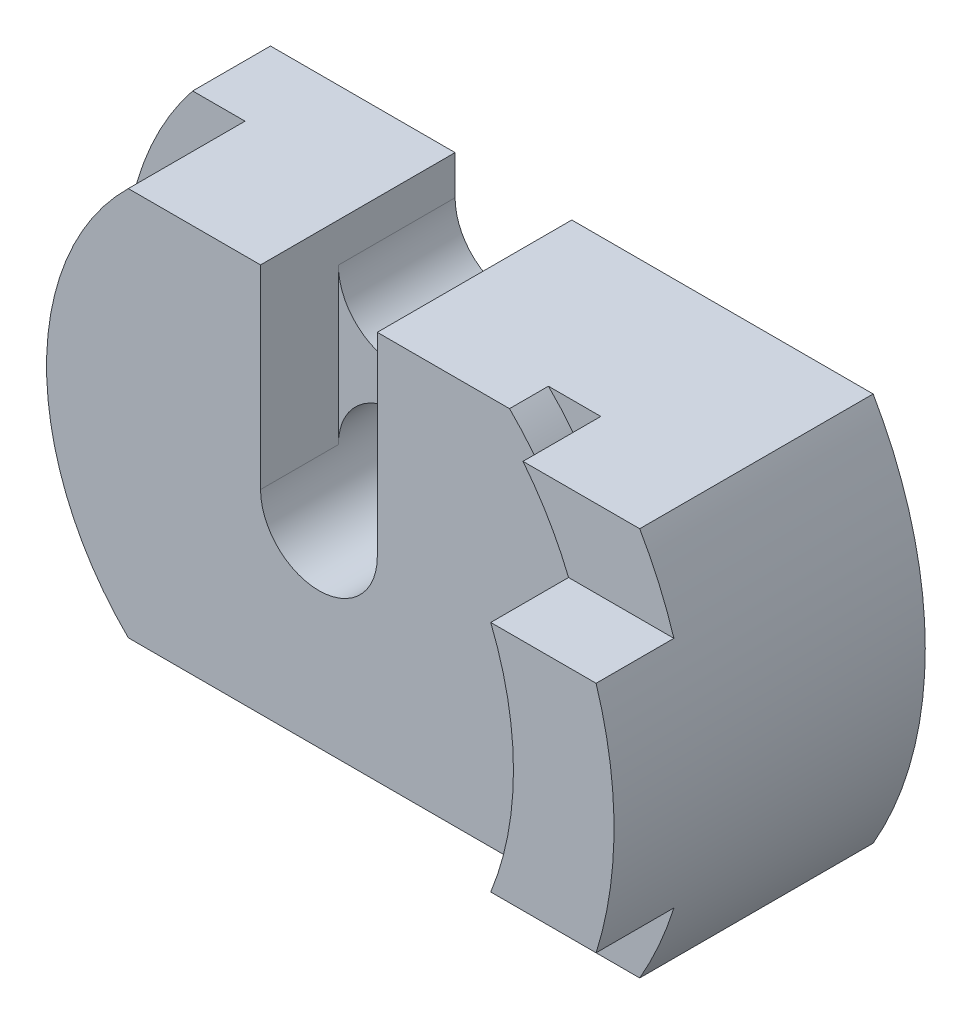
SolidWorks part; units mm, degrees
ref_plane "Front" through (0, 0, 0) normal (0, 0, 1) x (1, 0, 0)
ref_plane "Top" through (0, 0, 0) normal (0, 1, 0) x (1, 0, 0)
ref_plane "Right" through (0, 0, 0) normal (1, 0, 0) x (0, 0, -1)
sketch "Sketch1" plane through (0, 0, 0) normal (0, 0, 1) x (1, 0, 0)
  line L0 (-6.245, 5) -> (6.245, 5)
  line L1 (-6.245, -5) -> (6.245, -5)
  arc A0 (6.245, -5) -> (6.245, 5) centre (0, 0) ccw
  circle A2 centre (0, 0) radius 1.5
  arc A3 (-6.245, 5) -> (-6.245, -5) centre (0, 0) ccw
  dimension "D1" = 16
  dimension "D2" = 5
  dimension "D3" = 3
  dimension "D4" = 5
extrude "Boss-Extrude1" add sketch "Sketch1" along normal blind 2
sketch "Sketch2" plane through (0, 0, 2) normal (0, 0, 1) x (1, 0, 0)
  line L0 (6.245, 5) -> (-6.245, 5) construction
  line L1 (-6.245, -5) -> (6.245, -5) construction
  line L2 (-4.899, -5) -> (4.899, -5)
  line L3 (4.899, 5) -> (-4.899, 5)
  arc A0 (-4.899, 5) -> (-4.899, -5) centre (0, 0) ccw
  arc A1 (4.899, -5) -> (4.899, 5) centre (0, 0) ccw
  circle A2 centre (0, 0) radius 1.5
  point P3 (-4.899, 5)
  point P4 (4.899, 5)
  point P7 (4.899, -5)
  point P8 (-4.899, -5)
  dimension "D1" = 14
extrude "Boss-Extrude2" add sketch "Sketch2" along normal blind 3
sketch "Sketch3" plane through (0, 0, 0) normal (0, 0, -1) x (-1, 0, 0)
  line L0 (-6.245, -5) -> (-9.245, -5)
  line L1 (-6.245, 5) -> (-9.245, 5)
  arc A0 (-6.245, 5) -> (-6.245, -5) centre (0, 0) ccw
  arc A1 (-9.245, 5) -> (-9.245, -5) centre (-0.5847, 0) ccw
  dimension "D1" = 10
  dimension "D4" = 8
  dimension "D2" = 3
  dimension "D3" = 3
extrude "Boss-Extrude3" add sketch "Sketch3" against normal blind 6
sketch "Sketch4" plane through (0, 0, 6) normal (0, 0, 1) x (1, 0, 0)
  line L0 (7.4162, 3) -> (10.1241, 3)
  line L1 (7.4162, -3) -> (10.1241, -3)
  line L2 (6.245, 5) -> (9.245, 5) construction
  line L3 (9.245, -5) -> (6.245, -5) construction
  arc A0 (6.245, -5) -> (6.245, 5) centre (0, 0) ccw construction
  arc A1 (9.245, -5) -> (9.245, 5) centre (0.5847, 0) ccw construction
  arc A2 (10.1241, 3) -> (10.1241, -3) centre (0.5847, 0) cw
  arc A3 (7.4162, 3) -> (7.4162, -3) centre (0, 0) cw
  point P12 (7.745, 5)
  dimension "D1" = 2
  dimension "D2" = 2
extrude "Boss-Extrude4" add sketch "Sketch4" along normal blind 2
sketch "Sketch5" plane through (0, 0, 5) normal (0, 0, 1) x (1, 0, 0)
  line L0 (-1.5, 5) -> (-1.5, 0)
  line L1 (4.899, 5) -> (-4.899, 5) construction
  line L2 (1.5, 0) -> (1.5, 5)
  line L3 (1.5, 5) -> (-1.5, 5)
  circle A0 centre (0, 0) radius 1.5 construction
  arc A1 (-1.5, 0) -> (1.5, 0) centre (0, 0) ccw
  arc A2 (-1.5, 4) -> (1.5, 4) centre (0, 4) ccw
  line M8 (4.899, 5) -> (-4.899, 5)
  circle M9 centre (0, 0) radius 1.5
  dimension "D1" = 1.5
  dimension "D3" = 1.5
  dimension "D2" = 3
  dimension "D4" = 1
  dimension "D5" = 5
extrude "Cut-Extrude1" cut sketch "Sketch5" against normal blind 2 contours L0 A2 L2 M8 | A2 L0 L2 M9 | L0 M9
sketch "Sketch6" plane through (0, 0, 3) normal (0, 0, 1) x (1, 0, 0)
  line L0 (-1.5, 5) -> (1.5, 5)
  line L1 (1.5, 5) -> (1.5, 3.9952)
  line L2 (1.5, 0) -> (1.5, 5) construction
  line L3 (-1.5, 5) -> (-1.5, 0) construction
  line L4 (-1.5, 3.9952) -> (-1.5, 5)
  arc A0 (1.5, 3.9952) -> (-1.5, 3.9952) centre (0, 3.9952) cw
extrude "Cut-Extrude2" cut sketch "Sketch6" against normal blind 4
sketch "Sketch7" plane through (0, 0, 2) normal (0, 0, 1) x (1, 0, 0)
  line L0 (4.899, -5) -> (6.245, -5)
  line L1 (4.899, 5) -> (6.245, 5)
  arc A0 (4.899, 5) -> (4.899, -5) centre (0, 0) cw
  arc A1 (6.245, 5) -> (6.245, -5) centre (0, 0) cw
extrude "Boss-Extrude5" add sketch "Sketch7" along normal blind 2
